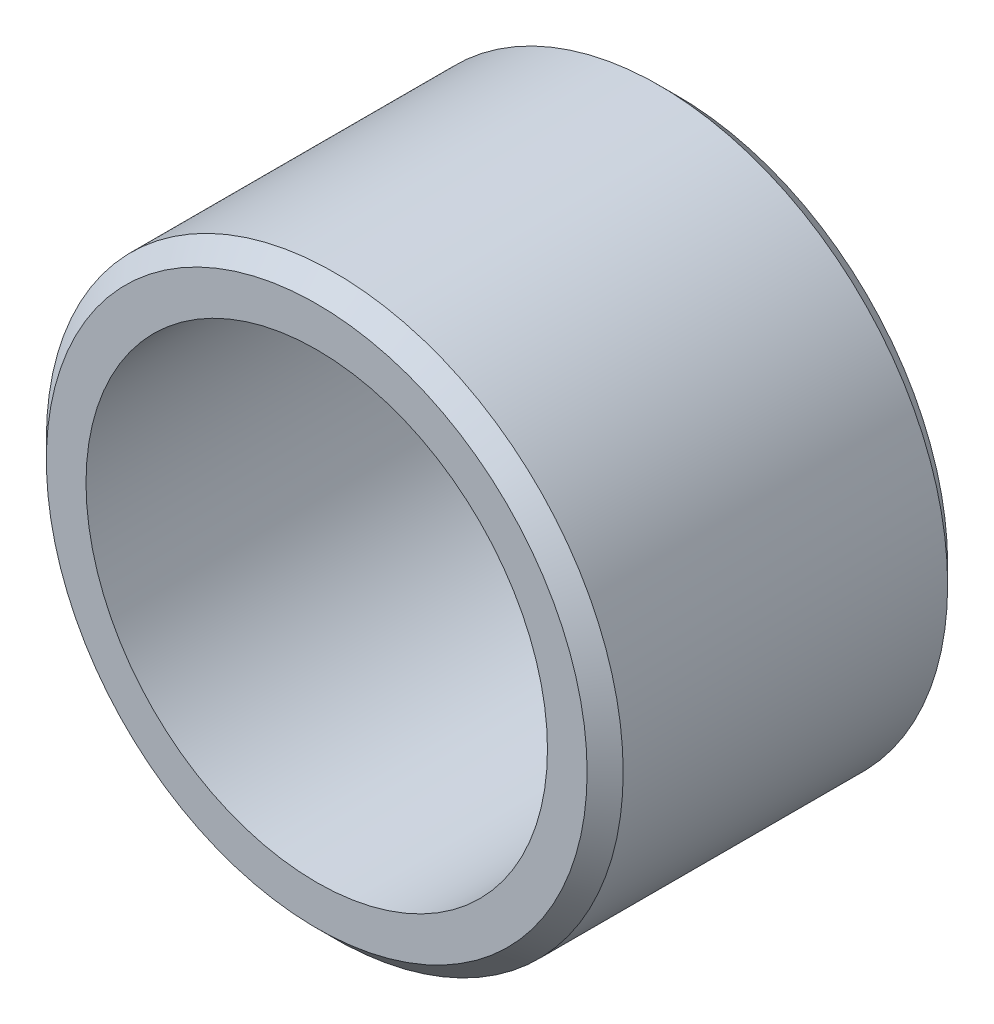
SolidWorks part; units mm, degrees
material "Copper"
ref_plane "Front Plane" through (0, 0, 0) normal (0, 0, 1) x (1, 0, 0)
ref_plane "Top Plane" through (0, 0, 0) normal (0, 1, 0) x (1, 0, 0)
ref_plane "Right Plane" through (0, 0, 0) normal (1, 0, 0) x (0, 0, -1)
sketch "Sketch1" plane through (0, 0, 0) normal (0, 0, 1) x (1, 0, 0)
  circle A0 centre (0, 0) radius 3.2
  circle A1 centre (0, 0) radius 4
  dimension "D1" = 6.4
  dimension "D2" = 8
extrude "Boss-Extrude1" add sketch "Sketch1" along normal blind 5
chamfer "Chamfer1" distance 0.25 angle 45 2 edges at (4, 0, 0) (4, 0, 5)
